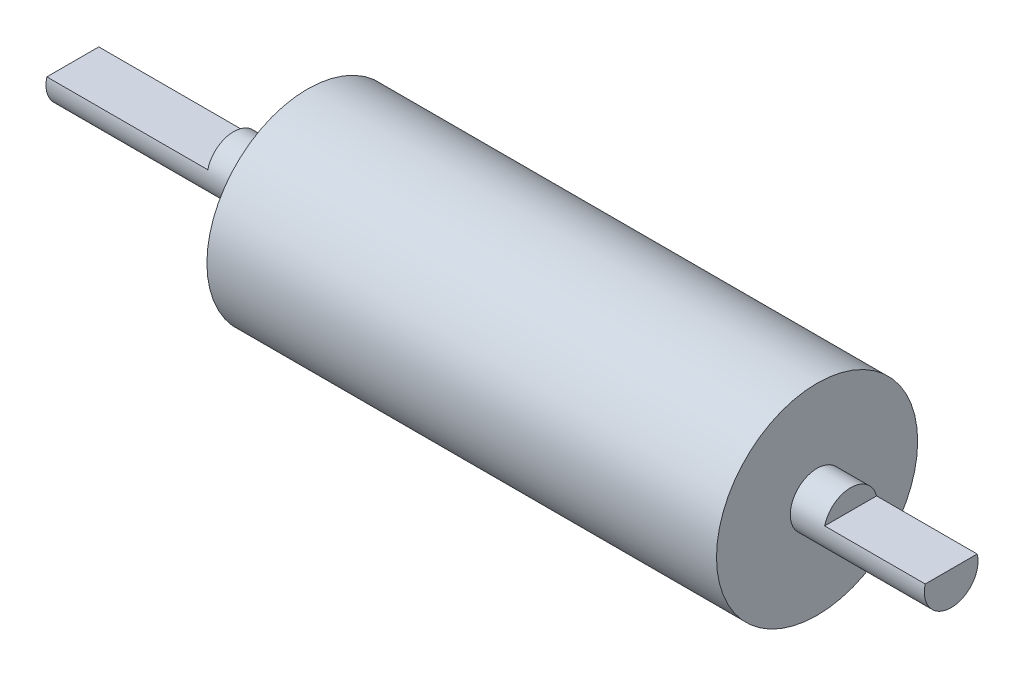
SolidWorks part; units mm, degrees
ref_plane "Plano frontal" through (0, 0, 0) normal (0, 0, 1) x (1, 0, 0)
ref_plane "Plano superior" through (0, 0, 0) normal (0, 1, 0) x (1, 0, 0)
ref_plane "Plano direito" through (0, 0, 0) normal (1, 0, 0) x (0, 0, -1)
sketch "Esboço8" plane through (0, 0, 0) normal (1, 0, 0) x (0, 0, -1)
  circle A0 centre (0, 0) radius 4
  dimension "D1" = 8
extrude "Ressalto-extrusão4" add sketch "Esboço8" along normal blind 35
sketch "Esboço9" plane through (35, 0, 0) normal (1, 0, 0) x (0, 0, -1)
  circle A0 centre (0, 0) radius 15
  dimension "D1" = 30
extrude "Ressalto-extrusão5" add sketch "Esboço9" along normal blind 76
sketch "Esboço10" plane through (111, 0, 0) normal (1, 0, 0) x (0, 0, -1)
  circle A0 centre (0, 0) radius 4
  dimension "D1" = 8
extrude "Ressalto-extrusão6" add sketch "Esboço10" along normal blind 20
sketch "Esboço11" plane through (0, 0, 0) normal (-1, 0, 0) x (0, 0, 1)
  line L2 (-5.544, 4) -> (5.544, 4)
  line L3 (-5.544, 4) -> (-5.544, 1)
  line L4 (-5.544, 1) -> (5.544, 1)
  line L5 (5.544, 4) -> (5.544, 1)
  circle A3 centre (0, 0) radius 4 construction
  dimension "D1" = 3
extrude "Corte-extrusão1" cut sketch "Esboço11" against normal blind 24
sketch "Esboço12" plane through (131, 0, 0) normal (1, 0, 0) x (0, 0, -1)
  line L2 (-9.5728, 4) -> (9.1906, 4)
  line L3 (-9.5728, 4) -> (-9.5728, 1)
  line L4 (-9.5728, 1) -> (9.1906, 1)
  line L5 (9.1906, 4) -> (9.1906, 1)
  circle A6 centre (0, 0) radius 4 construction
  dimension "D1" = 3
extrude "Corte-extrusão2" cut sketch "Esboço12" against normal blind 15
